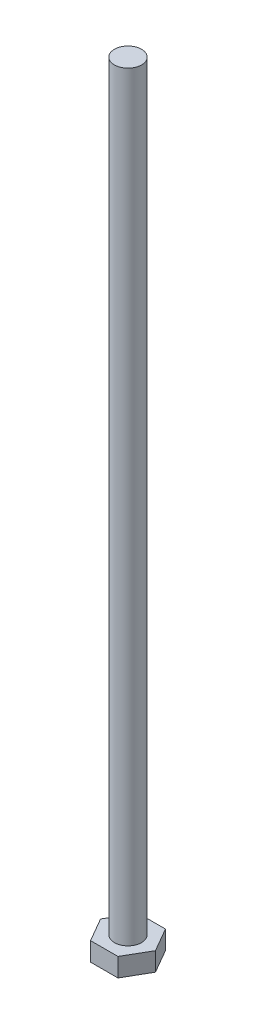
SolidWorks part; units mm, degrees
material "Alloy Steel"
ref_plane "Front Plane" through (0, 0, 0) normal (0, 0, 1) x (1, 0, 0)
ref_plane "Top Plane" through (0, 0, 0) normal (0, 1, 0) x (1, 0, 0)
ref_plane "Right Plane" through (0, 0, 0) normal (1, 0, 0) x (0, 0, -1)
sketch "Sketch1" plane through (0, 0, 0) normal (0, 1, 0) x (1, 0, 0)
  line L1 (6.4158, 0) -> (3.2079, 5.5562)
  line L2 (3.2079, 5.5562) -> (-3.2079, 5.5562)
  line L3 (-3.2079, 5.5562) -> (-6.4158, 0)
  line L4 (-6.4158, 0) -> (-3.2079, -5.5563)
  line L5 (-3.2079, -5.5563) -> (3.2079, -5.5562)
  line L6 (3.2079, -5.5562) -> (6.4158, 0)
  circle A0 centre (0, 0) radius 5.5562 construction
  dimension "D1" = 11.1125
extrude "Boss-Extrude1" add sketch "Sketch1" along normal blind 4.3656
sketch "Sketch2" plane through (0, 4.3656, 0) normal (0, 1, 0) x (1, 0, 0)
  circle A0 centre (0, 0) radius 3.175
  dimension "D1" = 6.35
extrude "Boss-Extrude2" add sketch "Sketch2" along normal blind 177.8
